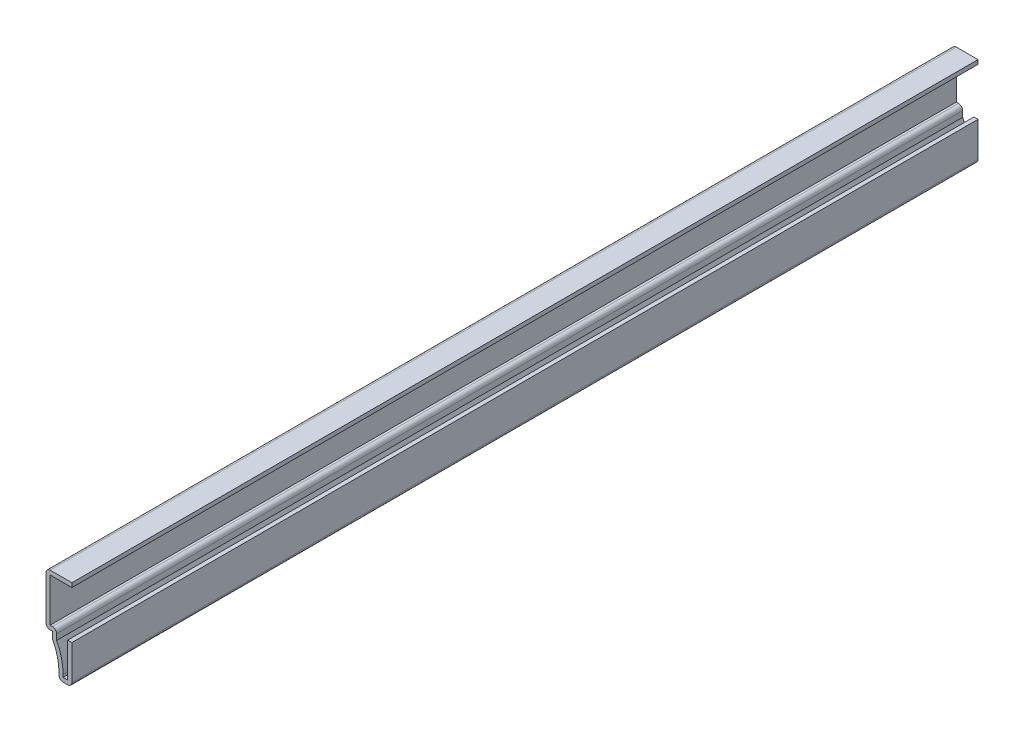
SolidWorks part; units mm, degrees
ref_plane "Front Plane" through (0, 0, 0) normal (0, 0, 1) x (1, 0, 0)
ref_plane "Top Plane" through (0, 0, 0) normal (0, 1, 0) x (1, 0, 0)
ref_plane "Right Plane" through (0, 0, 0) normal (1, 0, 0) x (0, 0, -1)
sketch "Sketch1" plane through (0, 0, 0) normal (0, 0, 1) x (1, 0, 0)
  line L0 (0, 0) -> (0, -9.525)
  line L1 (0, -9.525) -> (-3.175, -9.525)
  line L2 (-3.175, -9.525) -> (-3.175, -7.8367)
  line L3 (-4.7625, -1.6883) -> (-4.7625, 0)
  line L4 (-4.7625, 0) -> (-6.35, 0)
  line L5 (-6.35, 0) -> (-6.35, 12.7)
  line L6 (-6.35, 12.7) -> (0, 12.7)
  arc A0 (-3.175, -7.8367) -> (-4.7625, -1.6883) centre (-15.875, -7.8367) ccw
  point P10 (-4.7625, -0.8442)
  point P11 (0, 0)
  dimension "D5" = 12.7
  dimension "D1" = 9.525
  dimension "D2" = 3.175
  dimension "D3" = 1.5875
  dimension "D4" = 1.5875
  dimension "D6" = 6.35
  dimension "D7" = 22.225
  dimension "D8" = 12.7
extrude "Extrude-Thin1" add sketch "Sketch1" against normal blind 222.25 thin
fillet "Fillet1" radius 1.016 6 edges at (-6.35, 0, -111.125) (-3.7465, 1.016, -111.125) (-4.7625, -1.6883, -111.125) (-3.175, -9.525, -111.125) (0, -9.525, -111.125) (-6.35, 12.7, -111.125)
